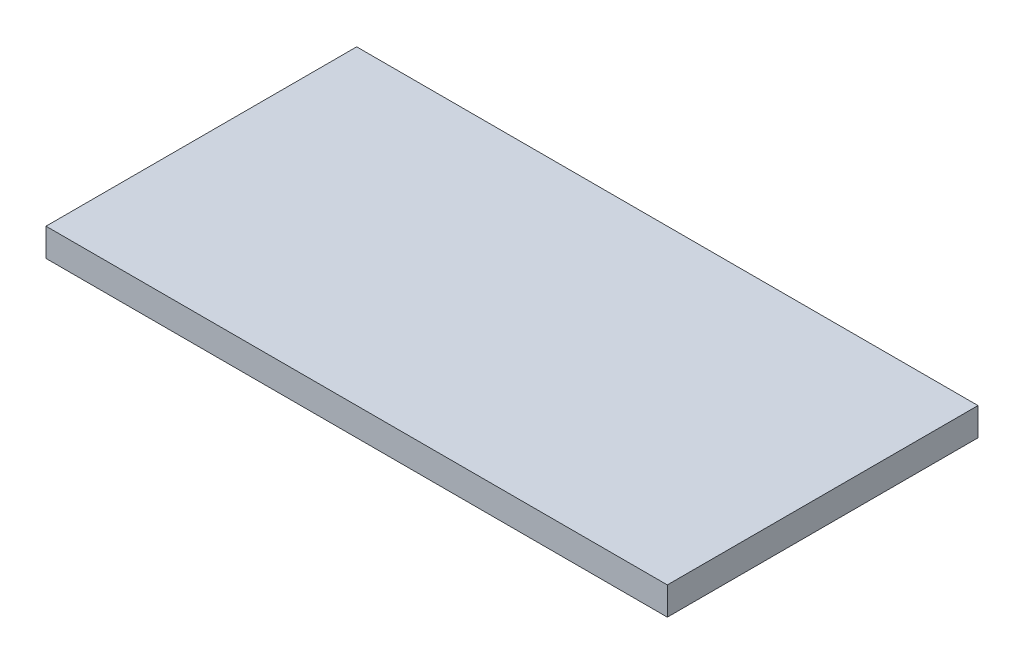
SolidWorks part; units mm, degrees
ref_plane "Front Plane" through (0, 0, 0) normal (0, 0, 1) x (1, 0, 0)
ref_plane "Top Plane" through (0, 0, 0) normal (0, 1, 0) x (1, 0, 0)
ref_plane "Right Plane" through (0, 0, 0) normal (1, 0, 0) x (0, 0, -1)
sketch "Sketch1" plane through (0, 0, 0) normal (0, 1, 0) x (1, 0, 0)
  line L1 (0, 0) -> (80, 0)
  line L2 (0, 0) -> (0, -40)
  line L3 (0, -40) -> (80, -40)
  line L4 (80, 0) -> (80, -40)
  dimension "D1" = 40
  dimension "D2" = 80
extrude "Boss-Extrude1" add sketch "Sketch1" along normal blind 3.6
